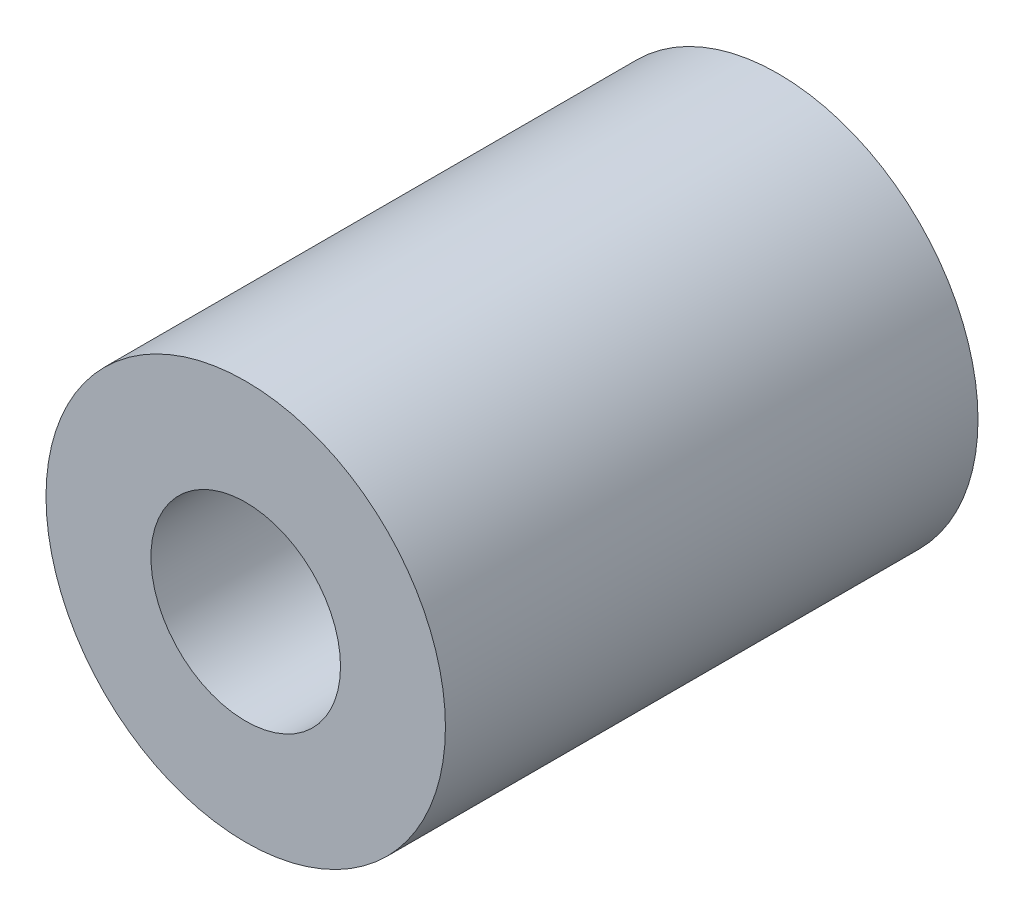
SolidWorks part; units mm, degrees
material "Brass"
ref_plane "Front Plane" through (0, 0, 0) normal (0, 0, 1) x (1, 0, 0)
ref_plane "Top Plane" through (0, 0, 0) normal (0, 1, 0) x (1, 0, 0)
ref_plane "Right Plane" through (0, 0, 0) normal (1, 0, 0) x (0, 0, -1)
sketch "Sketch1" plane through (0, 0, 0) normal (0, 0, 1) x (1, 0, 0)
  circle A0 centre (0, 0) radius 2.3813
  dimension "D1" = 4.7625
extrude "Boss-Extrude1" add sketch "Sketch1" along normal blind 6.35
hole_wizard "#4-40 Tapped Hole1" positions "Sketch2" profile "Sketch3" tap size "#4-40" standard "ANSI Inch" end condition through all
sketch "Sketch2" plane through (0, 0, 6.35) normal (0, 0, 1) x (1, 0, 0)
  point P0 (0, 0)
sketch "Sketch3" plane through (0, 0, 6.35) normal (1, 0, 0) x (0, -1, 0)
  line L0 (0, 0) -> (0, 6.35)
  line L1 (0, 6.35) -> (1.1303, 6.35)
  line L2 (1.1303, 6.35) -> (1.1303, 0)
  line L5 (1.1303, 0) -> (0, 0)
  line L11 (0, -6.35) -> (0, 107.95) construction
  dimension "Thru Tap Drill Dia." = 2.2606
  dimension "Thru Tap Drill Depth" = 6.35
cosmetic thread "Hole Thread1"
